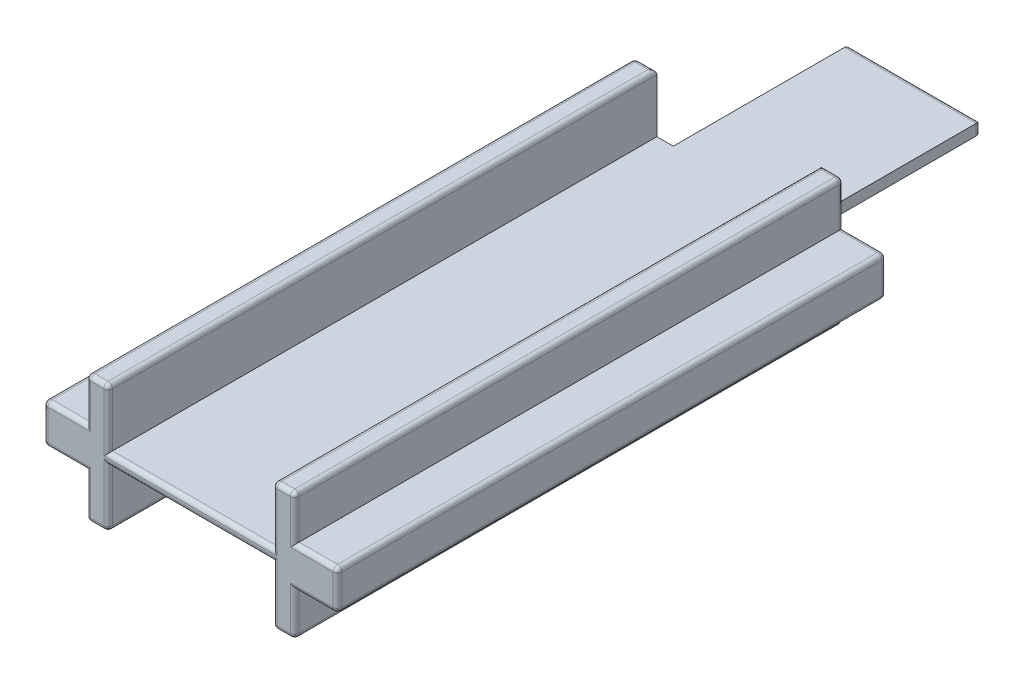
SolidWorks part; units mm, degrees
ref_plane "Ebene vorne" through (0, 0, 0) normal (0, 0, 1) x (1, 0, 0)
ref_plane "Ebene oben" through (0, 0, 0) normal (0, 1, 0) x (1, 0, 0)
ref_plane "Ebene rechts" through (0, 0, 0) normal (1, 0, 0) x (0, 0, -1)
sketch "Skizze1" plane through (0, 0, 0) normal (0, 0, 1) x (1, 0, 0)
  line L0 (-4.75, 0.9) -> (-6.7, 0.9)
  line L1 (6.7, -0.9) -> (4.75, -0.9)
  line L2 (6.7, -0.9) -> (6.7, 0.9)
  line L3 (6.7, 0.9) -> (4.75, 0.9)
  line L4 (-6.7, -0.9) -> (-6.7, 0.9)
  line L5 (6.7, -0.9) -> (-6.7, 0.9) construction
  line L6 (6.7, 0.9) -> (-6.7, -0.9) construction
  line L7 (-4.75, -2.9) -> (-3.75, -2.9)
  line L8 (-4.75, -2.9) -> (-4.75, -0.9)
  line L9 (-4.75, 2.9) -> (-3.75, 2.9)
  line L10 (-3.75, -2.9) -> (-3.75, -0.9)
  line L11 (-4.75, -2.9) -> (-3.75, 2.9) construction
  line L12 (-4.75, 2.9) -> (-3.75, -2.9) construction
  line L13 (4.75, -2.9) -> (3.75, -2.9)
  line L14 (4.75, -2.9) -> (4.75, -0.9)
  line L15 (4.75, 2.9) -> (3.75, 2.9)
  line L16 (3.75, -2.9) -> (3.75, -0.9)
  line L17 (4.75, -2.9) -> (3.75, 2.9) construction
  line L18 (4.75, 2.9) -> (3.75, -2.9) construction
  line L19 (-4.75, -0.9) -> (-6.7, -0.9)
  line L20 (-4.75, 0.9) -> (-4.75, 2.9)
  line L21 (-3.75, 0.9) -> (-3.75, 2.9)
  line L22 (3.75, -0.9) -> (-3.75, -0.9)
  line L23 (3.75, 0.9) -> (3.75, 2.9)
  line L24 (4.75, 0.9) -> (4.75, 2.9)
  line L25 (3.75, 0.9) -> (-3.75, 0.9)
  point P0 (0, 0)
  point P5 (-4.25, 0)
  point P11 (4.25, 0)
  dimension "D1" = 1.8
  dimension "D2" = 5.8
  dimension "D3" = 13.4
  dimension "D4" = 9.5
  dimension "D5" = 1
  dimension "D6" = 4.75
extrude "Aufsatz-Linear austragen1" add sketch "Skizze1" along normal blind 25
sketch "Skizze2" plane through (0, 0, 0) normal (0, 0, -1) x (-1, 0, 0)
  line L0 (-3.75, 0.9) -> (3.75, 0.9) construction
  line L1 (3, -0.9) -> (-3, -0.9)
  line L2 (3, -0.9) -> (3, 0.9)
  line L3 (3, 0.9) -> (-3, 0.9)
  line L4 (-3, -0.9) -> (-3, 0.9)
  line L5 (3, -0.9) -> (-3, 0.9) construction
  line L6 (3, 0.9) -> (-3, -0.9) construction
  point P0 (0, 0)
  dimension "D1" = 6
extrude "Aufsatz-Linear austragen2" add sketch "Skizze2" along normal blind 8
sketch "Skizze3" plane through (0, 0, 25) normal (0, 0, 1) x (1, 0, 0)
  line L1 (-3.75, -0.9) -> (3.75, -0.9)
  line L2 (-3.75, -0.9) -> (-3.75, -0.25)
  line L3 (-3.75, -0.25) -> (3.75, -0.25)
  line L4 (3.75, -0.9) -> (3.75, -0.25)
  line L5 (3.75, 0.9) -> (-3.75, 0.9)
  line L6 (3.75, 0.9) -> (3.75, 0.25)
  line L7 (3.75, 0.25) -> (-3.75, 0.25)
  line L8 (-3.75, 0.9) -> (-3.75, 0.25)
  dimension "D1" = 0.5
  dimension "D2" = 0.25
extrude "Schnitt-Linear austragen1" cut sketch "Skizze3" against normal through all
fillet "Verrundung1" radius 0.2 50 edges at (-5.725, 0.9, 25) (-4.75, 1.9, 25) (-3.75, 1.575, 25) (3.75, 1.575, 25) (4.75, 1.9, 25) (5.725, 0.9, 25) (5.725, -0.9, 25) (4.75, -1.9, 25) (3.75, -1.575, 25) (-3.75, -1.575, 25) (-4.75, -1.9, 25) (-5.725, -0.9, 25) (-3, 0, -8) (3, 0, -8) (-6.7, 0.9, 12.5) (-6.7, 0, 25) (-6.7, -0.9, 12.5) (-6.7, 0, 0) (6.7, -0.9, 12.5) (6.7, 0, 25) (6.7, 0.9, 12.5) (6.7, 0, 0) (-4.75, -2.9, 12.5) (-3.75, -2.9, 12.5) (-4.25, -2.9, 0) (3.75, -2.9, 12.5) (4.75, -2.9, 12.5) (4.25, -2.9, 0) (-3.75, 2.9, 12.5) (-4.75, 2.9, 12.5) (-4.25, 2.9, 0) (4.75, 2.9, 12.5) (3.75, 2.9, 12.5) (4.25, 2.9, 0) (4.75, 1.9, 0) (5.725, 0.9, 0) (5.725, -0.9, 0) (4.75, -1.9, 0) (-4.75, 1.9, 0) (-4.75, -1.9, 0) (-5.725, 0.9, 0) (-5.725, -0.9, 0) (-4.25, -2.9, 25) (4.25, -2.9, 25) (-4.25, 2.9, 25) (4.25, 2.9, 25) (0, 0.25, 25) (0, -0.25, 25) (0, 0.25, -8) (0, -0.25, -8)
